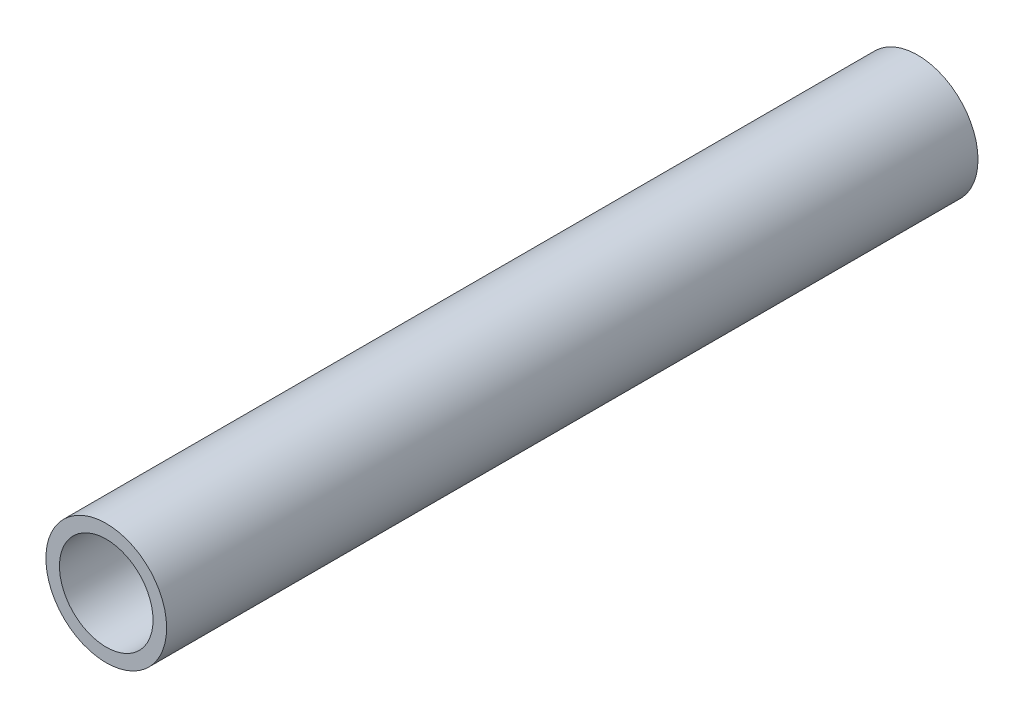
SolidWorks part; units mm, degrees
ref_plane "Front Plane" through (0, 0, 0) normal (0, 0, 1) x (1, 0, 0)
ref_plane "Top Plane" through (0, 0, 0) normal (0, 1, 0) x (1, 0, 0)
ref_plane "Right Plane" through (0, 0, 0) normal (1, 0, 0) x (0, 0, -1)
sketch "Sketch1" plane through (0, 0, 0) normal (0, 0, 1) x (1, 0, 0)
  circle A0 centre (0, 0) radius 50.8
  circle A1 centre (0, 0) radius 39.37
  dimension "D1" = 101.6
  dimension "D2" = 78.74
extrude "Boss-Extrude1" add sketch "Sketch1" along normal blind 682.752
